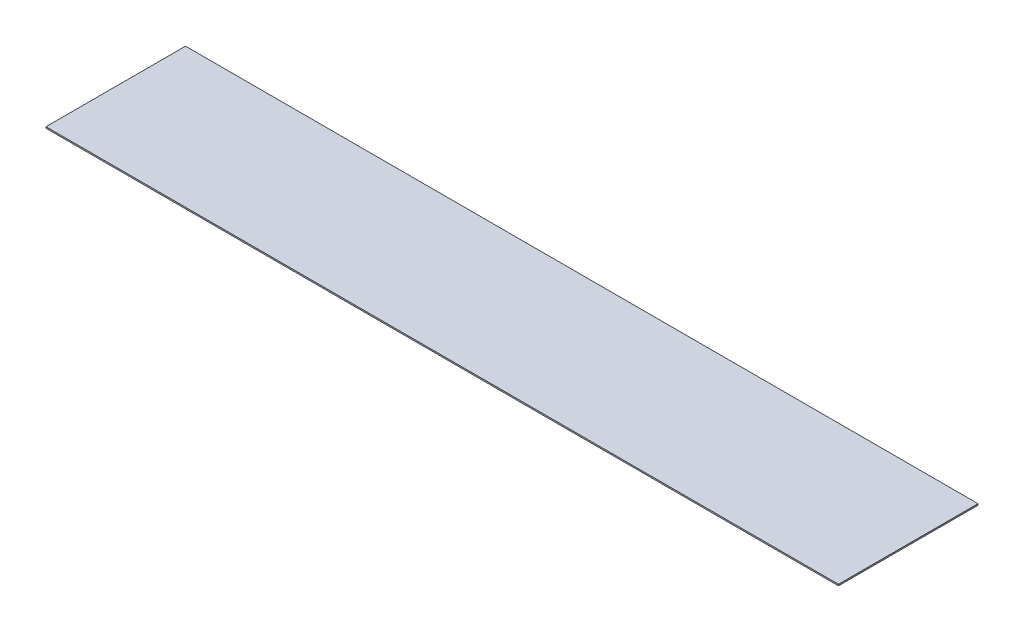
SolidWorks part; units mm, degrees
ref_plane "Front Plane" through (0, 0, 0) normal (0, 0, 1) x (1, 0, 0)
ref_plane "Top Plane" through (0, 0, 0) normal (0, 1, 0) x (1, 0, 0)
ref_plane "Right Plane" through (0, 0, 0) normal (1, 0, 0) x (0, 0, -1)
sketch "Sketch2" plane through (0, 0, 0) normal (0, 1, 0) x (1, 0, 0)
  line L1 (-2840, -500) -> (2840, -500)
  line L2 (-2840, -500) -> (-2840, 500)
  line L3 (-2840, 500) -> (2840, 500)
  line L4 (2840, -500) -> (2840, 500)
  line L5 (0, 500) -> (0, -500) construction
  line L6 (-2840, 0) -> (2840, 0) construction
  point P0 (0, 0)
  dimension "D1" = 5680
  dimension "D2" = 1000
extrude "Boss-Extrude1" add sketch "Sketch2" along normal blind 10
